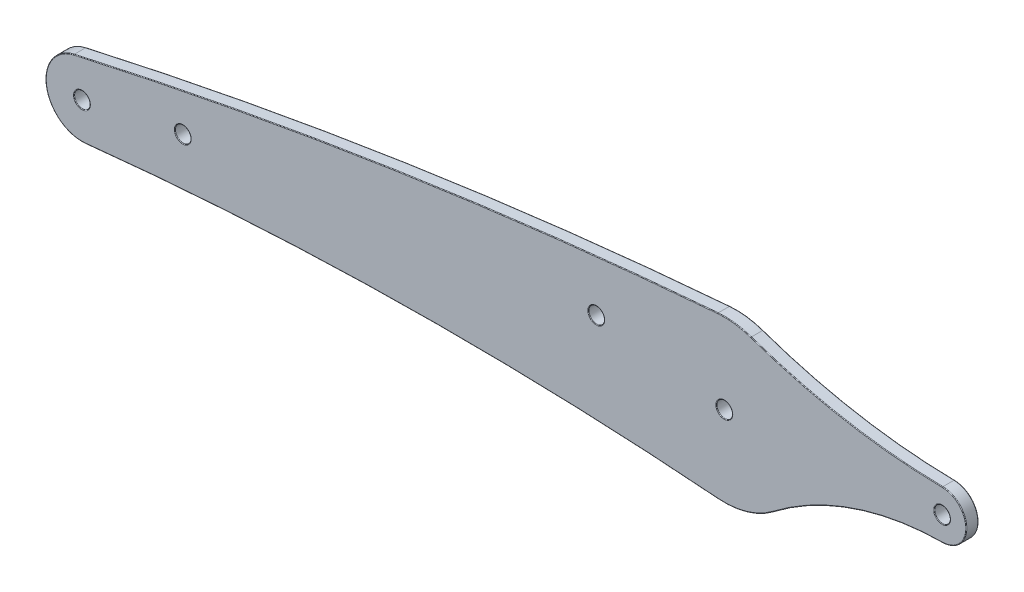
SolidWorks part; units mm, degrees
ref_plane "Płaszczyzna przednia" through (0, 0, 0) normal (0, 0, 1) x (1, 0, 0)
ref_plane "Płaszczyzna górna" through (0, 0, 0) normal (0, 1, 0) x (1, 0, 0)
ref_plane "Płaszczyzna prawa" through (0, 0, 0) normal (1, 0, 0) x (0, 0, -1)
sketch "Szkic1" plane through (0, 0, 0) normal (0, 0, 1) x (1, 0, 0)
  line L0 (-211.9431, 188.8447) -> (1.3329, 206.4325) construction
  line L1 (-211.9431, 188.8447) -> (1.3329, 206.4325) construction
  point P2 (-52.6671, 201.9794)
sketch "Szkic2" plane through (0, 0, 0) normal (0, 0, 1) x (1, 0, 0)
  circle A0 centre (-211.9431, 188.8447) radius 9 construction
  circle A1 centre (-52.6671, 201.9794) radius 20 construction
  circle A2 centre (-52.6671, 201.9794) radius 10 construction
  circle A3 centre (1.3329, 206.4325) radius 6 construction
  arc A4 (-213.9182, 197.6253) -> (-54.2799, 221.9143) centre (38.4557, -924.3406) cw
  arc A5 (-210.9906, 179.8953) -> (-54.2386, 182.0412) centre (-121.0285, -665.3306) cw
  arc A6 (-46.0538, 220.8544) -> (1.418, 212.4319) centre (3.5453, 362.4168) ccw
  arc A7 (-40.5333, 186.0806) -> (1.3805, 200.4327) centre (1.935, 130.4349) cw
  arc A8 (-54.2799, 221.9143) -> (-46.0538, 220.8544) centre (-52.6671, 201.9794) cw
  arc A9 (-213.9182, 197.6253) -> (-210.9906, 179.8953) centre (-211.9431, 188.8447) ccw
  arc A10 (-54.2386, 182.0412) -> (-40.5333, 186.0806) centre (-52.6671, 201.9794) ccw
  arc A11 (1.418, 212.4319) -> (1.3805, 200.4327) centre (1.3329, 206.4325) cw
  arc A12 (-211.9431, 188.8447) -> (1.3329, 206.4325) centre (-40.9765, -582.4337) cw construction
  point P27 (-186.9431, 193.9642)
  point P28 (-84.4171, 206.371)
  point P29 (0, 0)
  point P30 (0, 0)
  dimension "D1" = 12
  dimension "D2" = 40
  dimension "D3" = 20
  dimension "D4" = 18
  dimension "D5" = 850
  dimension "D6" = 1150
  dimension "D7" = 70
  dimension "D8" = 150
  dimension "D9" = 790
  dimension "D10" = 31.75
  dimension "D11" = 25
extrude "Dodanie-wyciągnięcie1" add sketch "Szkic2" against normal blind 3
hole_wizard "Otwór pod śrubę M3.51" positions "Szkic3" profile "Szkic4" hole size "M3.5" standard "ISO"
sketch "Szkic3" plane through (0, 0, 0) normal (0, 0, 1) x (1, 0, 0)
  point P0 (-211.9431, 188.8447)
  point P3 (-186.9431, 193.9642)
  point P6 (-84.4171, 206.371)
  point P9 (-52.6671, 201.9794)
  point P12 (1.3329, 206.4325)
sketch "Szkic4" plane through (-211.9431, 188.8447, 0) normal (1, 0, 0) x (0, -1, 0)
  line L0 (0, 0) -> (0, 11.1717)
  line L1 (0, 11.1717) -> (1.95, 10)
  line L2 (1.95, 10) -> (1.95, 0)
  line L5 (1.95, 0) -> (0, 0)
  line L10 (0, 11.1717) -> (-1.95, 10) construction
  line L11 (0, -6.35) -> (0, 107.95) construction
  dimension "Średnica otworu" = 3.9
  dimension "Głębokość otworu" = 10
  dimension "Kąt wiertła" = 118
fillet "Zaokrąglenie1" radius 0.15 26 edges at (-132.6642, 184.5897, -3) (-47.0129, 182.7953, -3) (-20.7418, 196.66, -3) (7.3329, 206.4137, -3) (-22.6585, 214.7234, -3) (-50.1113, 221.8154, -3) (-134.5259, 212.5752, -3) (-220.8229, 187.3785, -3) (3.2829, 206.4325, -3) (-50.7171, 201.9794, -3) (-82.4671, 206.371, -3) (-184.9931, 193.9642, -3) (-209.9931, 188.8447, -3) (-134.5259, 212.5752, 0) (-50.1113, 221.8154, 0) (-22.6585, 214.7234, 0) (7.3329, 206.4137, 0) (-20.7418, 196.66, 0) (-47.0129, 182.7953, 0) (-132.6642, 184.5897, 0) (-220.8229, 187.3785, 0) (3.2829, 206.4325, 0) (-50.7171, 201.9794, 0) (-82.4671, 206.371, 0) (-184.9931, 193.9642, 0) (-209.9931, 188.8447, 0)
